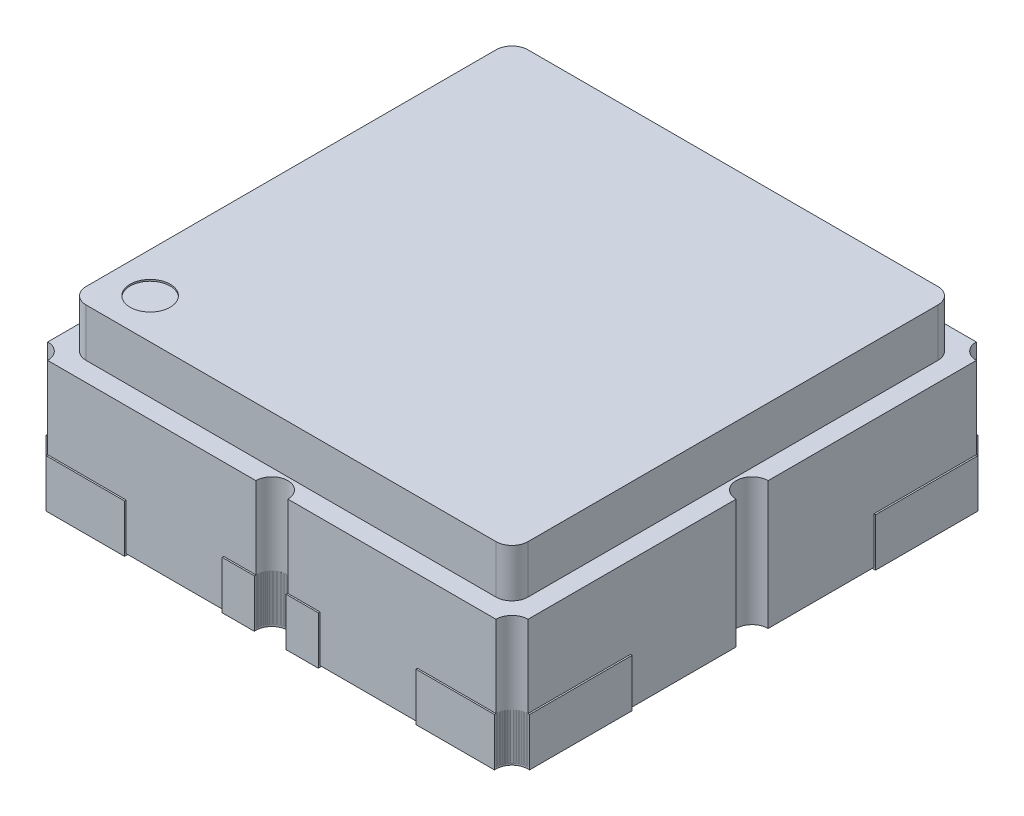
SolidWorks part; units mm, degrees
ref_plane "Front Plane" through (0, 0, 0) normal (0, 0, 1) x (1, 0, 0)
ref_plane "Top Plane" through (0, 0, 0) normal (0, 1, 0) x (1, 0, 0)
ref_plane "Right Plane" through (0, 0, 0) normal (1, 0, 0) x (0, 0, -1)
sketch "Sketch2" plane through (0, 0, 0) normal (0, 1, 0) x (1, 0, 0)
  line L1 (-1.5, -1.5) -> (1.5, -1.5)
  line L2 (-1.5, -1.5) -> (-1.5, 1.5)
  line L3 (-1.5, 1.5) -> (1.5, 1.5)
  line L4 (1.5, -1.5) -> (1.5, 1.5)
  line L5 (-1.5, -1.5) -> (1.5, 1.5) construction
  line L6 (-1.5, 1.5) -> (1.5, -1.5) construction
  point P0 (0, 0)
  dimension "D1" = 3
  dimension "D2" = 3
extrude "Boss-Extrude1" add sketch "Sketch2" along normal blind 0.8
sketch "Sketch3" plane through (0, 0.8, 0) normal (0, 1, 0) x (1, 0, 0)
  line L0 (0, 1.5) -> (0, -1.5) construction
  line L1 (1.5, 1.5) -> (-1.5, 1.5) construction
  line L2 (-1.5, -1.5) -> (1.5, -1.5) construction
  line L3 (-1.5, 0) -> (1.5, 0) construction
  line L4 (-1.5, 1.5) -> (-1.5, -1.5) construction
  line L5 (1.5, -1.5) -> (1.5, 1.5) construction
  circle A0 centre (-1.5, 1.5) radius 0.1
  circle A1 centre (0, 1.5) radius 0.1
  circle A2 centre (1.5, 1.5) radius 0.1
  circle A3 centre (-1.5, 0) radius 0.1
  circle A4 centre (1.5, 0) radius 0.1
  circle A5 centre (1.5, -1.5) radius 0.1
  circle A6 centre (0, -1.5) radius 0.1
  circle A7 centre (-1.5, -1.5) radius 0.1
  dimension "D1" = 0.2
  dimension "D5" = 1.5
  dimension "D2" = 3
  dimension "D4" = 2
sketch "Sketch4" plane through (0, 0.8, 0) normal (0, 1, 0) x (1, 0, 0)
  line L1 (-1.28, -1.38) -> (1.28, -1.38)
  line L2 (-1.38, -1.28) -> (-1.38, 1.28)
  line L3 (-1.28, 1.38) -> (1.28, 1.38)
  line L4 (1.38, -1.28) -> (1.38, 1.28)
  line L5 (-1.38, -1.38) -> (1.38, 1.38) construction
  line L6 (-1.38, 1.38) -> (1.38, -1.38) construction
  line L7 (1.5, 1.5) -> (-1.5, 1.5) construction
  line L8 (1.5, -1.5) -> (1.5, 1.5) construction
  line L9 (-1.5, 1.5) -> (-1.5, -1.5) construction
  line L10 (-1.5, -1.5) -> (1.5, -1.5) construction
  arc A0 (1.28, 1.38) -> (1.38, 1.28) centre (1.28, 1.28) cw
  arc A1 (1.28, -1.38) -> (1.38, -1.28) centre (1.28, -1.28) ccw
  arc A2 (-1.28, -1.38) -> (-1.38, -1.28) centre (-1.28, -1.28) cw
  arc A3 (-1.38, 1.28) -> (-1.28, 1.38) centre (-1.28, 1.28) cw
  dimension "D5" = 0.1
  dimension "D1" = 0.12
  dimension "D2" = 0.12
  dimension "D3" = 0.12
  dimension "D4" = 0.12
extrude "Boss-Extrude2" add sketch "Sketch4" along normal blind 0.3
sketch "Sketch5" plane through (0, 0, 0) normal (0, -1, 0) x (1, 0, 0)
  line L0 (-1.5, -1.5) -> (-1.5, 1.5) construction
  line L1 (-1.51, -1.51) -> (-0.91, -1.51)
  line L2 (-1.51, -1.51) -> (-1.51, -0.76)
  line L3 (-1.51, -0.76) -> (-0.91, -0.76)
  line L4 (-0.91, -1.51) -> (-0.91, -0.76)
  line L5 (1.5, -1.5) -> (-1.5, -1.5) construction
  line L6 (-1.5, 1.5) -> (1.5, 1.5) construction
  line L7 (-1.51, 1.51) -> (-0.91, 1.51)
  line L8 (-1.51, 1.51) -> (-1.51, 0.01)
  line L9 (-1.51, 0.01) -> (-0.91, 0.01)
  line L10 (-0.91, 1.51) -> (-0.91, 0.01)
  line L20 (0, 0) -> (1.5, 0) construction
  line L21 (0, -1.5) -> (0, 1.5) construction
  line L30 (-0.3, -1.51) -> (-0.3, -0.76)
  line L31 (-0.3, -1.51) -> (0.3, -1.51)
  line L32 (0.3, -1.51) -> (0.3, -0.76)
  line L33 (-0.3, -0.76) -> (0.3, -0.76)
  line L34 (0.91, -1.51) -> (0.91, -0.76)
  line L35 (0.91, -1.51) -> (1.51, -1.51)
  line L36 (1.51, -1.51) -> (1.51, -0.76)
  line L37 (0.91, -0.76) -> (1.51, -0.76)
  line L38 (1.5, 1.5) -> (1.5, -1.5) construction
  line L39 (0.91, 1.51) -> (1.51, 1.51)
  line L40 (1.51, 1.51) -> (1.51, 0.76)
  line L41 (0.91, 0.76) -> (1.51, 0.76)
  line L42 (0.91, 1.51) -> (0.91, 0.76)
  line L43 (-0.3, 1.51) -> (0.3, 1.51)
  line L44 (0.3, 1.51) -> (0.3, 0.76)
  line L45 (-0.3, 0.76) -> (0.3, 0.76)
  line L46 (-0.3, 1.51) -> (-0.3, 0.76)
  dimension "D1" = 0.01
  dimension "D2" = 0.01
  dimension "D3" = 0.75
  dimension "D4" = 0.6
  dimension "D5" = 0.01
  dimension "D6" = 0.01
  dimension "D7" = 0.6
  dimension "D8" = 1.5
  dimension "D10" = 0.01
  dimension "D9" = 3
extrude "Boss-Extrude3" add sketch "Sketch5" against normal blind 0.3 from offset 0.01 separate body
extrude "Cut-Extrude1" cut sketch "Sketch3" against normal through all
sketch "Sketch6" plane through (0, 1.1, 0) normal (0, 1, 0) x (1, 0, 0)
  line L0 (-1.38, 1.28) -> (-1.38, -1.28) construction
  line L1 (-1.28, -1.38) -> (1.28, -1.38) construction
  circle A0 centre (-1.13, -1.13) radius 0.125
  dimension "D1" = 0.25
  dimension "D2" = 0.25
  dimension "D3" = 0.25
extrude "Cut-Extrude2" cut sketch "Sketch6" against normal blind 0.01
